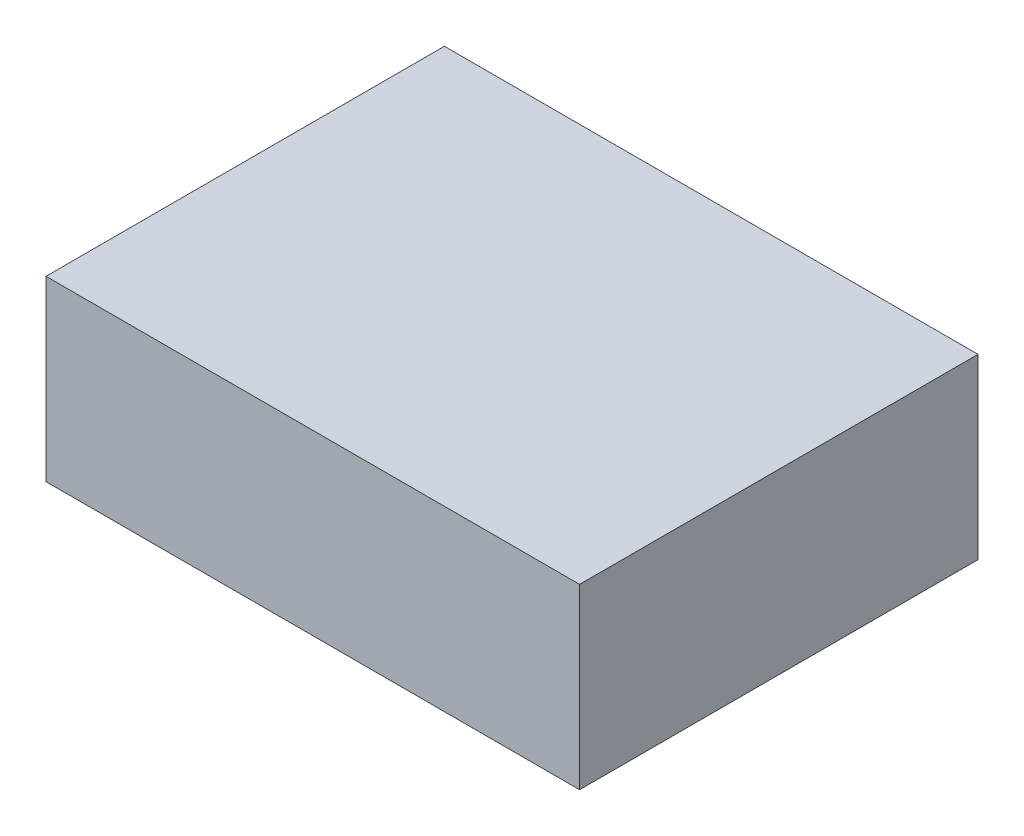
SolidWorks part; units mm, degrees
ref_plane "Front Plane" through (0, 0, 0) normal (0, 0, 1) x (1, 0, 0)
ref_plane "Top Plane" through (0, 0, 0) normal (0, 1, 0) x (1, 0, 0)
ref_plane "Right Plane" through (0, 0, 0) normal (1, 0, 0) x (0, 0, -1)
sketch "Sketch1" plane through (0, 0, 0) normal (0, 1, 0) x (1, 0, 0)
  line L1 (0, 0) -> (95.25, 0)
  line L2 (0, 0) -> (0, 71.12)
  line L3 (0, 71.12) -> (95.25, 71.12)
  line L4 (95.25, 0) -> (95.25, 71.12)
  dimension "D1" = 95.25
  dimension "D2" = 71.12
extrude "Boss-Extrude1" add sketch "Sketch1" along normal blind 31.75
